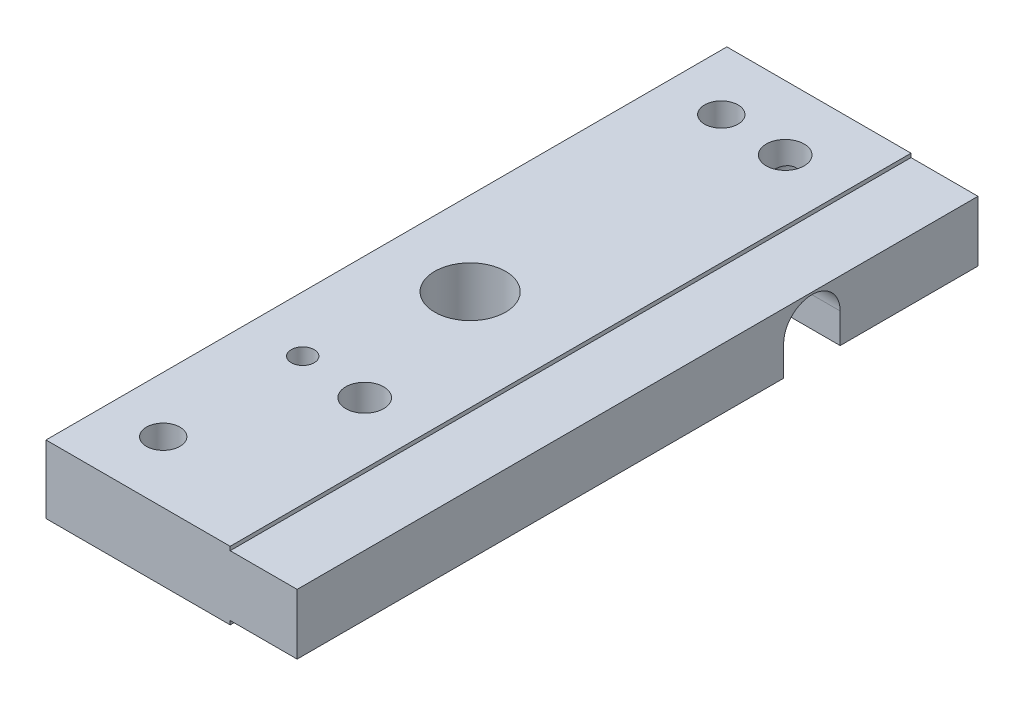
SolidWorks part; units mm, degrees
material "2024-T3"
ref_plane "Front Plane" through (0, 0, 0) normal (0, 0, 1) x (1, 0, 0)
ref_plane "Top Plane" through (0, 0, 0) normal (0, 1, 0) x (1, 0, 0)
ref_plane "Right Plane" through (0, 0, 0) normal (1, 0, 0) x (0, 0, -1)
sketch "Sketch1" plane through (0, 0, 0) normal (1, 0, 0) x (0, 0, -1)
  line L1 (0, -3.05) -> (61, -3.05)
  line L2 (0, -3.05) -> (0, 3.05)
  line L3 (0, 3.05) -> (61, 3.05)
  line L4 (61, -3.05) -> (61, 3.05)
  dimension "D1" = 61
  dimension "D2" = 6.1
extrude "Boss-Extrude1" add sketch "Sketch1" along normal blind 22.5
sketch "Sketch2" plane through (22.5, 0, 0) normal (1, 0, 0) x (0, 0, -1)
  line L0 (0, 3.05) -> (0, -3.05) construction
  line L1 (0, -2.7064) -> (61, -2.7064)
  line L2 (0, -2.7064) -> (0, 2.7064)
  line L3 (0, 2.7064) -> (61, 2.7064)
  line L4 (61, -2.7064) -> (61, 2.7064)
  line L5 (61, -3.05) -> (61, 3.05) construction
  line L7 (30.5, 3.05) -> (30.5, -3.05) construction
  line L8 (61, 3.05) -> (0, 3.05) construction
  line L9 (0, -3.05) -> (61, -3.05) construction
  line L10 (30.5, 0) -> (0, 0) construction
  dimension "D1" = 5.4128
extrude "Cut-Extrude1" cut sketch "Sketch2" against normal blind 6 flip side to cut
sketch "Sketch5" plane through (0, 0, 0) normal (-1, 0, 0) x (0, 0, 1)
  line L0 (-46.119, -0.019) -> (0, -0.019) construction
  line L2 (0, 3.05) -> (0, -3.05) construction
  line L3 (0, -3.05) -> (-61, -3.05) construction
  line L4 (-43.5866, -0.019) -> (-43.5866, -3.05)
  line L5 (-43.5866, -3.05) -> (-48.6514, -3.05)
  line L6 (-48.6514, -3.05) -> (-48.6514, -0.019)
  line L7 (-61, -3.05) -> (-61, 3.05) construction
  line L8 (-61, 2.7064) -> (0, 2.7064) construction
  arc A0 (-43.5866, -0.019) -> (-48.6514, -0.019) centre (-46.119, -0.019) ccw
  dimension "D1" = 5.0648
  dimension "D2" = 14.881
  dimension "D3" = 2.7254
extrude "Cut-Extrude3" cut sketch "Sketch5" against normal through all
sketch "Sketch6" plane through (0, 3.05, 0) normal (0, 1, 0) x (1, 0, 0)
  line L0 (0, 30.5) -> (22.5, 30.5) construction
  line L2 (22.5, 61) -> (22.5, 0) construction
  line L7 (0, 61) -> (0, 0) construction
  circle A0 centre (7.5, 30.5) radius 3.175
  dimension "D2" = 6.35
  dimension "D1" = 7.5
extrude "Cut-Extrude4" cut sketch "Sketch6" against normal through all
sketch "Sketch7" plane through (0, 3.05, 0) normal (0, 1, 0) x (1, 0, 0)
  line L0 (5, 61) -> (5, 0) construction
  line L1 (16.5, 61) -> (0, 61) construction
  line L2 (16.5, 0) -> (0, 0) construction
  line L3 (0, 61) -> (0, 0) construction
  line L4 (0, 30.5) -> (22.5, 30.5) construction
  line L5 (22.5, 61) -> (22.5, 0) construction
  circle A0 centre (5, 55.5) radius 1.5
  circle A1 centre (5, 5.5) radius 1.5
  dimension "D1" = 3
  dimension "D2" = 5
  dimension "D3" = 25
  dimension "D4" = 25
extrude "Cut-Extrude5" cut sketch "Sketch7" against normal through all
hole_wizard "M2.5x0.45 Tapped Hole1" positions "Sketch11" profile "Sketch10" tap size "M2.5x0.45" standard "ANSI Metric" end condition through all
sketch "Sketch11" plane through (0, -3.05, 0) normal (0, -1, 0) x (-1, 0, 0)
  line L0 (-5, 5.5) -> (-5, 18) construction
  point P0 (-5, 18)
  dimension "D1" = 12.5
sketch "Sketch10" plane through (5, -3.05, -18) normal (1, 0, 0) x (0, 0, -1)
  line L0 (0, 0) -> (0, 6.1)
  line L1 (0, 6.1) -> (1.025, 6.1)
  line L2 (1.025, 6.1) -> (1.025, 0)
  line L5 (1.025, 0) -> (0, 0)
  line L11 (0, -6.35) -> (0, 107.95) construction
  dimension "Thru Tap Drill Dia." = 2.05
  dimension "Thru Tap Drill Depth" = 6.1
cosmetic thread "Hole Thread1" parameters "D2"=2.5
hole_wizard "M2.5x0.45 Tapped Hole2" positions "Sketch13" profile "Sketch12" tap size "M2.5x0.45" standard "ANSI Metric"
sketch "Sketch13" plane through (0, 0, -61) normal (0, 0, -1) x (-1, 0, 0)
  line L0 (-10, 0) -> (0, 0) construction
  point P0 (-10, 0)
  dimension "D1" = 10
sketch "Sketch12" plane through (10, 0, -61) normal (1, 0, 0) x (0, 1, 0)
  line L0 (0, 0) -> (0, 7.9159)
  line L1 (0, 7.9159) -> (1.025, 7.3)
  line L2 (1.025, 7.3) -> (1.025, 0)
  line L5 (1.025, 0) -> (0, 0)
  line L10 (0, 7.9159) -> (-1.025, 7.3) construction
  line L11 (0, -6.35) -> (0, 107.95) construction
  dimension "Tap Drill Dia." = 2.05
  dimension "Tap Drill Depth" = 7.3
  dimension "Drill Angle" = 118
cosmetic thread "Hole Thread2" parameters "D1"=5, "D2"=2.5
hole_wizard "CBORE for M3 Pan Head Machine Screw1" positions "Sketch15" profile "Sketch14" counterbore size "M3" standard "ANSI Metric" end condition through all
sketch "Sketch15" plane through (0, -3.05, 0) normal (0, -1, 0) x (-1, 0, 0)
  line L0 (-16.5, 61) -> (0, 61) construction
  point P0 (-11, 55.228)
  point P2 (-11, 17.553)
  dimension "D1" = 37.675
  dimension "D2" = 5.772
sketch "Sketch14" plane through (11, -3.05, -55.228) normal (1, 0, 0) x (0, 0, -1)
  line L0 (0, 0) -> (0, 6.1)
  line L1 (0, 6.1) -> (1.7, 6.1)
  line L3 (1.7, 6.1) -> (1.7, 2.2)
  line L4 (1.7, 2.2) -> (3.25, 2.2)
  line L5 (3.25, 2.2) -> (3.25, 0)
  line L7 (3.25, 0) -> (0, 0)
  line L11 (0, -6.35) -> (0, 107.95) construction
  dimension "Thru Hole Dia." = 3.4
  dimension "Thru Hole Depth" = 6.1
  dimension "C'Bore Dia." = 6.5
  dimension "C'Bore Depth" = 2.2
